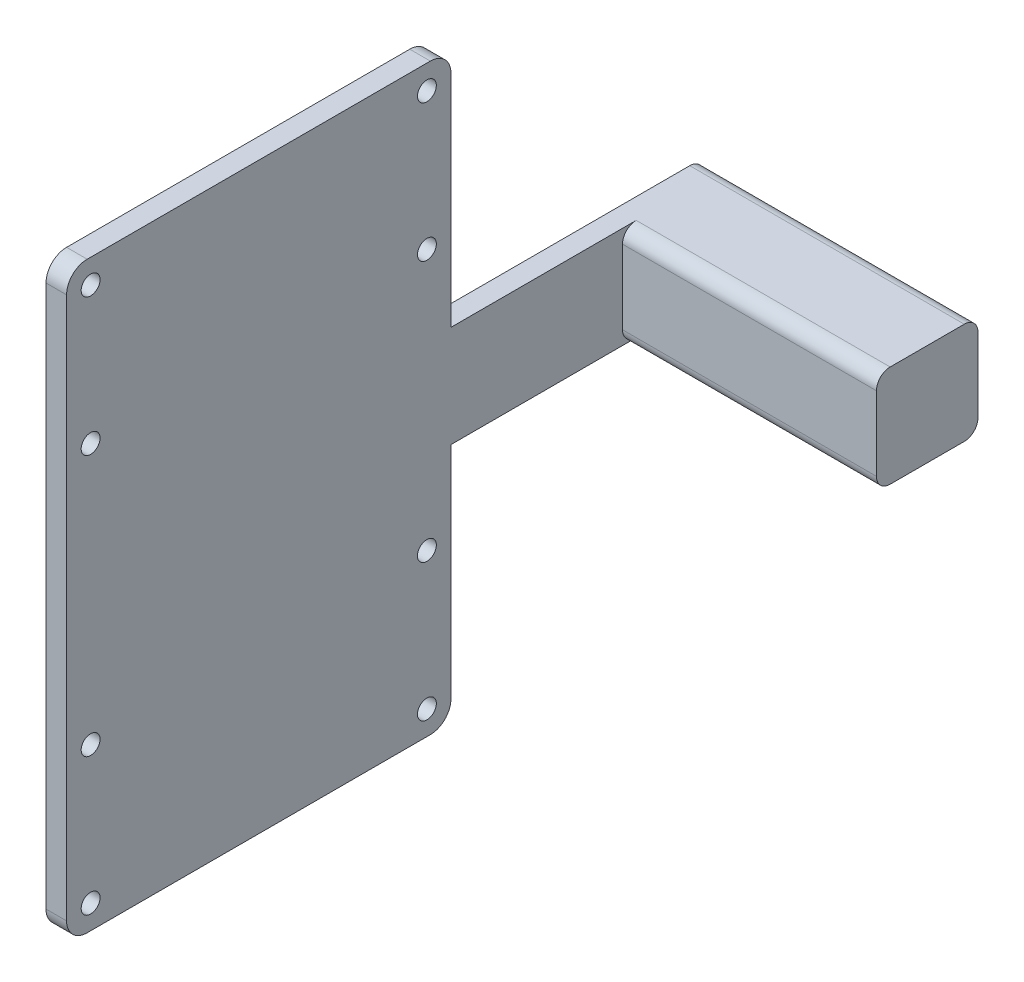
SolidWorks part; units mm, degrees
ref_plane "Front Plane" through (0, 0, 0) normal (0, 0, 1) x (1, 0, 0)
ref_plane "Top Plane" through (0, 0, 0) normal (0, 1, 0) x (1, 0, 0)
ref_plane "Right Plane" through (0, 0, 0) normal (1, 0, 0) x (0, 0, -1)
sketch "Sketch1" plane through (0, 0, 0) normal (0, 0, 1) x (1, 0, 0)
  line L1 (20, -7.4) -> (-20, -7.4)
  line L2 (20, -7.4) -> (20, 7.4)
  line L3 (20, 7.4) -> (-20, 7.4)
  line L4 (-20, -7.4) -> (-20, 7.4)
  line L5 (20, -7.4) -> (-20, 7.4) construction
  line L6 (20, 7.4) -> (-20, -7.4) construction
  point P0 (0, 0)
  dimension "D1" = 14.8
  dimension "D2" = 40
extrude "Boss-Extrude1" add sketch "Sketch1" along normal blind 14.8
sketch "Sketch3" plane through (0, 0, 14.8) normal (0, 0, 1) x (1, 0, 0)
  line L0 (-20, -7.4) -> (20, -7.4) construction
  line L1 (-20, 7.4) -> (-17, 7.4)
  line L2 (-20, 7.4) -> (-20, -7.4)
  line L3 (-20, -7.4) -> (-17, -7.4)
  line L4 (-17, 7.4) -> (-17, -7.4)
  dimension "D1" = 3
extrude "Boss-Extrude3" add sketch "Sketch3" along normal blind 25
sketch "Sketch5" plane through (0, 0, 39.8) normal (0, 0, 1) x (1, 0, 0)
  line L0 (-17, -7.4) -> (-17, 7.4) construction
  line L1 (-20, -42.5) -> (-17, -42.5)
  line L2 (-20, -42.5) -> (-20, 42.5)
  line L3 (-20, 42.5) -> (-17, 42.5)
  line L4 (-17, -42.5) -> (-17, 42.5)
  line L5 (-20, 7.4) -> (-20, -7.4) construction
  line L6 (-17, 0) -> (-20, 0) construction
  line L7 (-17, 0) -> (-20, 0) construction
  dimension "D1" = 85
extrude "Boss-Extrude4" add sketch "Sketch5" along normal blind 56
sketch "Sketch6" plane through (-17, 0, 0) normal (1, 0, 0) x (0, 0, -1)
  line L0 (-95.8, -42.5) -> (-95.8, 42.5) construction
  line L1 (-95.8, 42.5) -> (-39.8, 42.5) construction
  circle A0 centre (-92.3, 39) radius 1.375
  circle A1 centre (-43.3, 39) radius 1.375
  circle A2 centre (-43.3, -19) radius 1.375
  circle A3 centre (-92.3, -19) radius 1.375
  dimension "D1" = 2.75
  dimension "D2" = 2.75
  dimension "D3" = 2.75
  dimension "D4" = 2.75
  dimension "D5" = 49
  dimension "D6" = 58
  dimension "D7" = 3.5
  dimension "D8" = 3.5
extrude "Cut-Extrude1" cut sketch "Sketch6" against normal blind 5
fillet "Fillet2" radius 3 4 edges at (-18.5, -42.5, 39.8) (-18.5, -42.5, 95.8) (-18.5, 42.5, 39.8) (-18.5, 42.5, 95.8)
mirror "Mirror1" about plane through (0, 0, 0) normal (0, 1, 0) of "Cut-Extrude1"
fillet "Fillet3" radius 2 4 edges at (1.5, -7.4, 14.8) (1.5, 7.4, 14.8) (0, 7.4, 0) (0, -7.4, 0)
